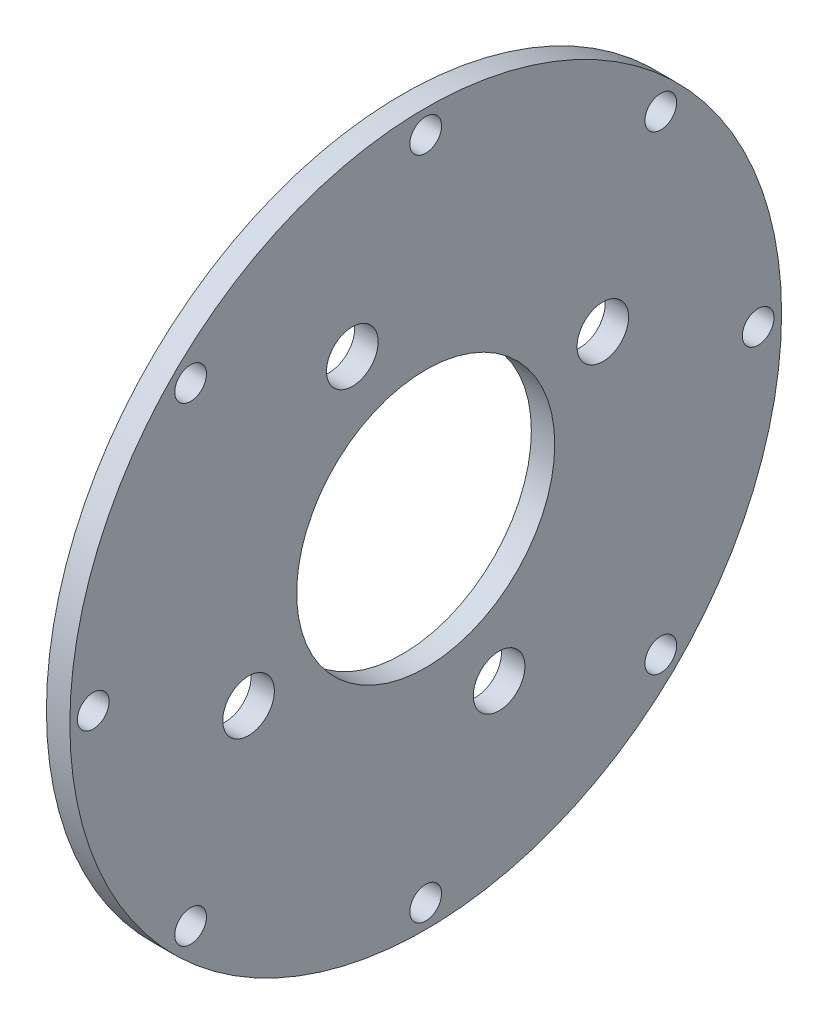
SolidWorks part; units mm, degrees
ref_plane "Front Plane" through (0, 0, 0) normal (0, 0, 1) x (1, 0, 0)
ref_plane "Top Plane" through (0, 0, 0) normal (0, 1, 0) x (1, 0, 0)
ref_plane "Right Plane" through (0, 0, 0) normal (1, 0, 0) x (0, 0, -1)
sketch "Sketch1" plane through (0, 0, 0) normal (1, 0, 0) x (0, 0, -1)
  line L0 (9.9498, 24.0209) -> (0, 0) construction
  line L2 (24.0182, 9.948) -> (-24.0238, -9.9508) construction
  line L3 (0, 0) -> (-4.1204, 9.948) construction
  line L4 (0, 0) -> (-13.6375, 5.6491) construction
  circle A0 centre (0, 0) radius 17.5 construction
  circle A1 centre (0, 0) radius 48.26
  circle A2 centre (0, 45.085) radius 2.1527
  circle A3 centre (-24.0238, -9.9508) radius 3.5
  circle A4 centre (31.8799, 31.8799) radius 2.1527
  circle A5 centre (45.085, 0) radius 2.1527
  circle A6 centre (24.0182, 9.948) radius 3.5
  circle A7 centre (-9.9504, 24.024) radius 3.5
  circle A8 centre (31.8799, -31.8799) radius 2.1526
  circle A9 centre (0, -45.085) radius 2.1527
  circle A10 centre (-31.8799, -31.8799) radius 2.1526
  circle A11 centre (-45.085, 0) radius 2.1526
  circle A12 centre (-31.8799, 31.8799) radius 2.1526
  circle A13 centre (0, 0) radius 17.5
  circle A14 centre (9.951, -24.0242) radius 3.5
  dimension "D1" = 96.52
  dimension "D2" = 4.3053
  dimension "D4" = 26
  dimension "D5" = 35
  dimension "D6" = 7
  dimension "D7" = 7
  dimension "D3" = 45.085
  dimension "D8" = 52
  dimension "D9" = 45
extrude "Boss-Extrude1" add sketch "Sketch1" along normal blind 3.175
